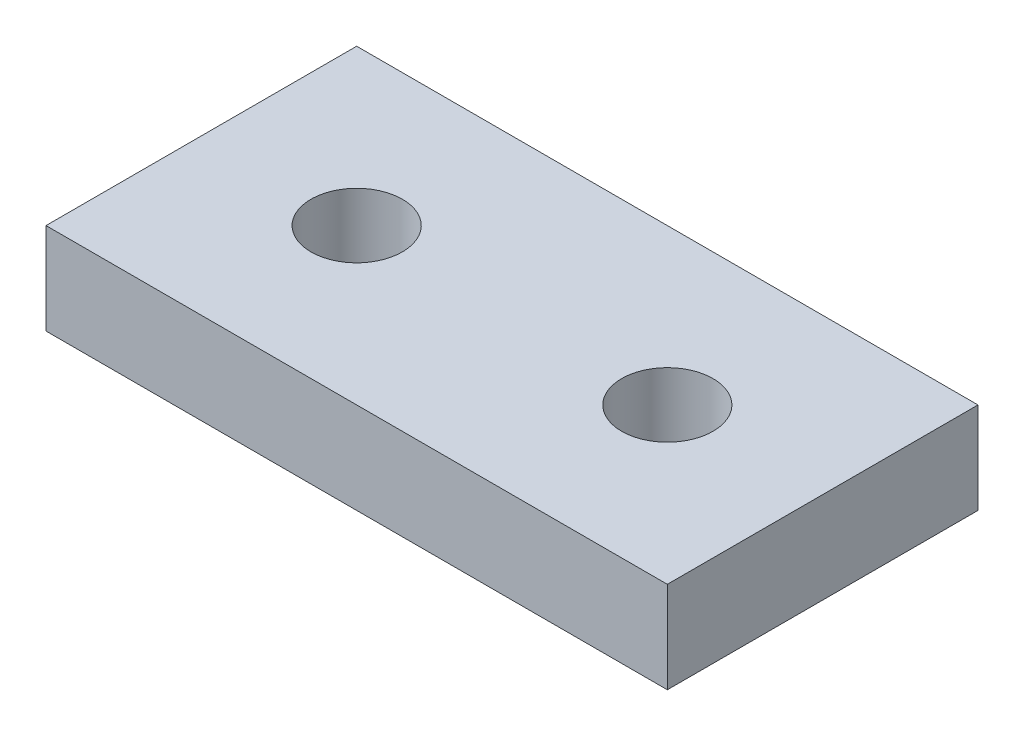
SolidWorks part; units mm, degrees
ref_plane "Front Plane" through (0, 0, 0) normal (0, 0, 1) x (1, 0, 0)
ref_plane "Top Plane" through (0, 0, 0) normal (0, 1, 0) x (1, 0, 0)
ref_plane "Right Plane" through (0, 0, 0) normal (1, 0, 0) x (0, 0, -1)
other "Configuration Table"
sketch "sketch1" plane through (0, 0, 0) normal (0, 1, 0) x (1, 0, 0)
  line L0 (0, -8.5) -> (8.5, -8.5) construction
  line L1 (0, 0) -> (34, 0)
  line L2 (0, 0) -> (0, -17)
  line L3 (0, -17) -> (34, -17)
  line L4 (34, 0) -> (34, -17)
  line L5 (8.5, -8.5) -> (25.5, -8.5) construction
  circle A1 centre (8.5, -8.5) radius 2.5
  circle A2 centre (25.5, -8.5) radius 2.5
  dimension "D4" = 5
  dimension "D1" = 17
  dimension "D2" = 34
  dimension "D3" = 8.5
  dimension "D6" = 17
  dimension "D5" = 2
extrude "Boss-Extrude1" add sketch "sketch1" along normal blind 5
equation "\"D2@sketch1\" = \"length\""
equation "\"holes\" = 2"
equation "\"cdist\"= 17mm'centre distance between holes"
equation "\"width\"= 17mm"
equation "\"length\"= \"cdist\" * \"holes\""
equation "\"D1@sketch1\" = \"width\""
equation "\"hdiam\"= 5mm'Hole diametre"
equation "\"D4@sketch1\" = \"hdiam\""
equation "\"D6@sketch1\" = \"cdist\""
equation "\"D5@sketch1\" = \"holes\""
equation "\"D1@Boss-Extrude1\"=\"height\""
equation "\"height\"= 5mm'Height of extrude"
